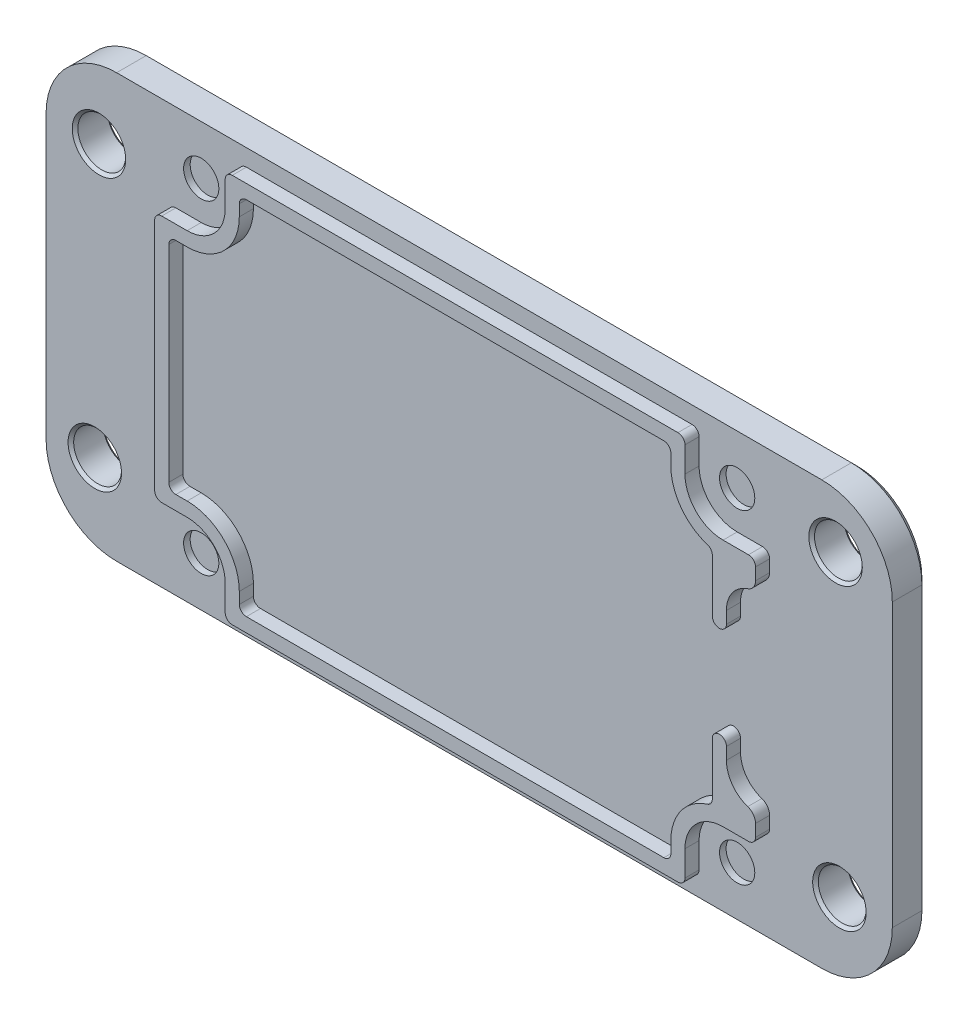
SolidWorks part; units mm, degrees
ref_plane "Plane XZ" through (0, 0, 0) normal (0, 0, 1) x (1, 0, 0)
ref_plane "Plane XY" through (0, 0, 0) normal (0, 1, 0) x (1, 0, 0)
ref_plane "Plane YZ" through (0, 0, 0) normal (1, 0, 0) x (0, 0, -1)
sketch "Sketch1" plane through (0, 0, 0) normal (0, 0, 1) x (1, 0, 0)
  line L0 (0, 19.05) -> (0, -19.05) construction
  line L1 (-38.1, 19.05) -> (38.1, 19.05)
  line L2 (-38.1, 19.05) -> (-38.1, -19.05)
  line L3 (-38.1, -19.05) -> (38.1, -19.05)
  line L4 (38.1, 19.05) -> (38.1, -19.05)
  dimension "D1" = 76.2
  dimension "D2" = 38.1
extrude "Boss-Extrude1" add sketch "Sketch1" along normal blind 3.175
sketch "Sketch2" plane through (0, 0, 3.175) normal (0, 0, 1) x (1, 0, 0)
  line L0 (0, 17.78) -> (0, -17.78) construction
  line L1 (-27.305, 17.78) -> (27.305, 17.78) construction
  line L2 (-27.305, 17.78) -> (-27.305, -17.78) construction
  line L3 (-27.305, -17.78) -> (27.305, -17.78) construction
  line L4 (27.305, 17.78) -> (27.305, -17.78) construction
  line L5 (-27.305, -11.43) -> (-24.13, -11.43)
  line L6 (-20.955, -14.605) -> (-20.955, -17.78)
  line L7 (-27.305, 0) -> (0, 0) construction
  line L8 (27.305, 17.78) -> (27.305, 8.255) construction
  line L9 (24.6862, 8.255) -> (27.305, 8.255) construction
  line L10 (24.6862, 8.255) -> (24.6862, -8.255) construction
  line L11 (27.305, -8.255) -> (24.6862, -8.255) construction
  line L12 (27.305, -8.255) -> (27.305, -17.78) construction
  line L13 (27.305, -11.43) -> (24.13, -11.43)
  line L14 (20.955, -14.605) -> (20.955, -17.78)
  line L15 (-27.305, 11.43) -> (-24.13, 11.43)
  line L16 (-20.955, 14.605) -> (-20.955, 17.78)
  line L17 (27.305, 11.43) -> (24.13, 11.43)
  line L18 (20.955, 14.605) -> (20.955, 17.78)
  line L19 (-20.955, 17.78) -> (20.955, 17.78)
  line L20 (-27.305, -11.43) -> (-27.305, 11.43)
  line L21 (-20.955, -17.78) -> (20.955, -17.78)
  line L22 (27.305, -11.43) -> (27.305, -8.255) construction
  line L23 (27.305, 8.255) -> (27.305, 11.43) construction
  line L24 (27.305, 11.43) -> (27.305, 9.4613)
  line L26 (27.305, -9.4613) -> (27.305, -11.43)
  line L27 (24.6862, -5.8423) -> (24.6862, 5.8423)
  arc A0 (-24.13, -11.43) -> (-20.955, -14.605) centre (-24.13, -14.605) cw
  circle A1 centre (-24.13, -14.605) radius 1.5875 construction
  arc A6 (24.13, -11.43) -> (20.955, -14.605) centre (24.13, -14.605) ccw
  circle A7 centre (24.13, -14.605) radius 1.5875 construction
  arc A8 (-24.13, 11.43) -> (-20.955, 14.605) centre (-24.13, 14.605) ccw
  arc A9 (24.13, 11.43) -> (20.955, 14.605) centre (24.13, 14.605) cw
  circle A10 centre (24.13, 14.605) radius 1.5875 construction
  circle A11 centre (-24.13, 14.605) radius 1.5875 construction
  arc A16 (27.305, 9.4613) -> (26.4321, 8.255) centre (26.035, 9.4613) cw
  arc A17 (26.4321, 8.255) -> (24.6862, 5.8423) centre (27.2262, 5.8423) ccw
  arc A18 (27.305, -9.4613) -> (26.4321, -8.255) centre (26.035, -9.4613) ccw
  arc A19 (26.4321, -8.255) -> (24.6862, -5.8423) centre (27.2262, -5.8423) cw
  point P21 (27.305, -8.255)
  point P24 (27.305, 8.255)
  point P27 (24.6862, 8.255)
  point P30 (24.6862, -8.255)
  dimension "D5" = 3.175
  dimension "D6" = 29.21
  dimension "D7" = 48.26
  dimension "D8" = 3.175
  dimension "D12" = 1.27
  dimension "D13" = 2.54
  dimension "D1" = 54.61
  dimension "D2" = 35.56
  dimension "D3" = 22.86
  dimension "D4" = 41.91
  dimension "D9" = 16.51
  dimension "D10" = 2.6188
sketch "Sketch4" plane through (0, 0, 3.175) normal (0, 0, 1) x (1, 0, 0)
  circle A0 centre (24.13, -14.605) radius 1.5875 construction
  circle A1 centre (24.13, 14.605) radius 1.5875 construction
  circle A2 centre (-24.13, 14.605) radius 1.5875 construction
  circle A3 centre (-24.13, -14.605) radius 1.5875 construction
  circle A4 centre (24.13, -14.605) radius 1.5875
  circle A5 centre (24.13, 14.605) radius 1.5875
  circle A6 centre (-24.13, 14.605) radius 1.5875
  circle A7 centre (-24.13, -14.605) radius 1.5875
extrude "Cut-Extrude1" cut sketch "Sketch4" against normal through all
hole_wizard "CBORE for #2 Pan Head Machine Screw1" positions "Sketch6" profile "Sketch7" counterbore size "#2" standard "ANSI Inch" end condition through all
sketch "Sketch6" plane through (0, 0, 0) normal (0, 0, -1) x (-1, 0, 0)
  circle A0 centre (-24.13, -14.605) radius 1.5875 construction
  circle A1 centre (24.13, -14.605) radius 1.5875 construction
  point P0 (-24.13, 14.605)
  point P3 (-24.13, -14.605)
  point P5 (24.13, -14.605)
  point P7 (24.13, 14.605)
sketch "Sketch7" plane through (24.13, 14.605, 0) normal (1, 0, 0) x (0, 1, 0)
  line L0 (0, 0) -> (0, 3.175)
  line L1 (0, 3.175) -> (1.3525, 3.175)
  line L3 (1.3525, 3.175) -> (1.3525, 2.0828)
  line L4 (2.3812, 2.0828) -> (1.3525, 2.0828)
  line L5 (2.3812, 2.0828) -> (2.3813, 0.3287)
  line L6 (2.3813, 0.3287) -> (2.667, 0)
  line L7 (2.667, 0) -> (0, 0)
  line L8 (-2.3813, 0.3287) -> (-2.667, 0) construction
  line L11 (0, -6.35) -> (0, 107.95) construction
  dimension "Thru Hole Dia." = 2.7051
  dimension "Thru Hole Depth" = 3.175
  dimension "C'Bore Dia." = 4.7625
  dimension "C'Bore Depth" = 2.0828
  dimension "Near C'Sink Dia." = 5.334
  dimension "Near C'Sink Angle" = 82
sketch "Sketch5" plane through (0, 0, 3.175) normal (0, 0, 1) x (1, 0, 0)
  line L0 (19.431, 14.605) -> (19.431, 16.256)
  line L1 (19.431, 16.256) -> (-19.431, 16.256)
  line L2 (-19.431, 16.256) -> (-19.431, 14.605)
  line L3 (-24.13, 9.906) -> (-25.781, 9.906)
  line L4 (-25.781, 9.906) -> (-25.781, -9.906)
  line L5 (-25.781, -9.906) -> (-24.13, -9.906)
  line L6 (-19.431, -14.605) -> (-19.431, -16.256)
  line L7 (-19.431, -16.256) -> (19.431, -16.256)
  line L8 (19.431, -16.256) -> (19.431, -14.605)
  line L9 (23.1622, -10.0068) -> (23.1622, 10.0068)
  line L28 (-27.051, 11.176) -> (-27.051, -11.176)
  line L29 (-27.051, -11.176) -> (-24.13, -11.176)
  line L30 (-20.701, -14.605) -> (-20.701, -17.526)
  line L31 (-20.701, -17.526) -> (20.701, -17.526)
  line L32 (20.701, -17.526) -> (20.701, -14.605)
  line L33 (24.13, -11.176) -> (27.051, -11.176)
  line L34 (27.051, -11.176) -> (27.051, -9.4613)
  line L35 (24.4322, -5.8423) -> (24.4322, 5.8423)
  line L36 (27.051, 9.4613) -> (27.051, 11.176)
  line L37 (27.051, 11.176) -> (24.13, 11.176)
  line L38 (20.701, 14.605) -> (20.701, 17.526)
  line L39 (20.701, 17.526) -> (-20.701, 17.526)
  line L40 (-20.701, 17.526) -> (-20.701, 14.605)
  line L41 (-24.13, 11.176) -> (-27.051, 11.176)
  line L42 (-27.051, 11.176) -> (-27.051, -11.176)
  line L43 (-27.051, -11.176) -> (-24.13, -11.176)
  line L44 (-20.701, -14.605) -> (-20.701, -17.526)
  line L45 (-20.701, -17.526) -> (20.701, -17.526)
  line L46 (20.701, -17.526) -> (20.701, -14.605)
  line L47 (24.13, -11.176) -> (27.051, -11.176)
  line L48 (27.051, -11.176) -> (27.051, -9.4613)
  line L49 (24.4322, -5.8423) -> (24.4322, 5.8423)
  line L50 (27.051, 9.4613) -> (27.051, 11.176)
  line L51 (27.051, 11.176) -> (24.13, 11.176)
  line L52 (20.701, 14.605) -> (20.701, 17.526)
  line L53 (20.701, 17.526) -> (-20.701, 17.526)
  line L54 (-20.701, 17.526) -> (-20.701, 14.605)
  line L55 (-24.13, 11.176) -> (-27.051, 11.176)
  arc A0 (-24.13, 9.906) -> (-19.431, 14.605) centre (-24.13, 14.605) ccw
  arc A1 (-19.431, -14.605) -> (-24.13, -9.906) centre (-24.13, -14.605) ccw
  arc A2 (19.431, 14.605) -> (23.1622, 10.0068) centre (24.13, 14.605) ccw
  arc A3 (19.431, -14.605) -> (23.1622, -10.0068) centre (24.13, -14.605) cw
  arc A16 (-20.701, -14.605) -> (-24.13, -11.176) centre (-24.13, -14.605) ccw
  arc A17 (24.13, -11.176) -> (20.701, -14.605) centre (24.13, -14.605) ccw
  arc A18 (27.051, -9.4613) -> (26.3526, -8.4963) centre (26.035, -9.4613) ccw
  arc A19 (24.4322, -5.8423) -> (26.3526, -8.4963) centre (27.2262, -5.8423) ccw
  arc A20 (26.3526, 8.4963) -> (24.4322, 5.8423) centre (27.2262, 5.8423) ccw
  arc A21 (26.3526, 8.4963) -> (27.051, 9.4613) centre (26.035, 9.4613) ccw
  arc A22 (20.701, 14.605) -> (24.13, 11.176) centre (24.13, 14.605) ccw
  arc A23 (-24.13, 11.176) -> (-20.701, 14.605) centre (-24.13, 14.605) ccw
  arc A24 (-20.701, -14.605) -> (-24.13, -11.176) centre (-24.13, -14.605) ccw
  arc A25 (24.13, -11.176) -> (20.701, -14.605) centre (24.13, -14.605) ccw
  arc A26 (27.051, -9.4613) -> (26.3526, -8.4963) centre (26.035, -9.4613) ccw
  arc A27 (24.4322, -5.8423) -> (26.3526, -8.4963) centre (27.2262, -5.8423) ccw
  arc A28 (26.3526, 8.4963) -> (24.4322, 5.8423) centre (27.2262, 5.8423) ccw
  arc A29 (26.3526, 8.4963) -> (27.051, 9.4613) centre (26.035, 9.4613) ccw
  arc A30 (20.701, 14.605) -> (24.13, 11.176) centre (24.13, 14.605) ccw
  arc A31 (-24.13, 11.176) -> (-20.701, 14.605) centre (-24.13, 14.605) ccw
  dimension "D3" = 1.27
  dimension "D1" = 0.254
  dimension "D2" = 1.27
extrude "Boss-Extrude3" add sketch "Sketch5" along normal blind 1.27 contours A31 L55 L42 L43 A24 L44 L45 L46 A25 L47 L48 A26 A27 L49 A28 A29 L50 L51 A30 L52 L53 L54 A3 L8 L7 L6 A1 L5 L4 L3 A0 L2 L1 L0 A2 L9
fillet "Fillet1" radius 6.35 4 edges at (38.1, -19.05, 1.5875) (38.1, 19.05, 1.5875) (-38.1, 19.05, 1.5875) (-38.1, -19.05, 1.5875)
fillet "Fillet2" radius 0.635 8 edges at (-20.701, 17.526, 3.81) (-27.051, 11.176, 3.81) (-27.051, -11.176, 3.81) (-20.701, -17.526, 3.81) (27.051, -11.176, 3.81) (20.701, -17.526, 3.81) (20.701, 17.526, 3.81) (27.051, 11.176, 3.81)
fillet "Fillet3" radius 0.635 8 edges at (-25.781, -9.906, 3.81) (-19.431, -16.256, 3.81) (19.431, -16.256, 3.81) (23.1622, -10.0068, 3.81) (23.1622, 10.0068, 3.81) (19.431, 16.256, 3.81) (-25.781, 9.906, 3.81) (-19.431, 16.256, 3.81)
hole_wizard "#6 Clearance Hole1" positions "Sketch9" profile "Sketch10" hole size "#6" standard "ANSI Inch" end condition through all
sketch "Sketch9" plane through (0, 0, 3.175) normal (0, 0, 1) x (1, 0, 0)
  line L1 (-33.3375, 12.7) -> (33.3375, 12.7) construction
  line L2 (-33.3375, 12.7) -> (-33.3375, -12.7) construction
  line L3 (-33.3375, -12.7) -> (33.3375, -12.7) construction
  line L4 (33.3375, 12.7) -> (33.3375, -12.7) construction
  line L5 (-38.1, 12.7) -> (-38.1, -12.7) construction
  line L6 (-33.3375, 0) -> (33.3375, 0) construction
  point P0 (-33.3375, 12.7)
  point P2 (-33.7144, -11.9542)
  point P4 (32.9919, 14.0391)
  point P6 (33.3375, -12.7)
  dimension "D1" = 4.7625
  dimension "D2" = 25.4
sketch "Sketch10" plane through (-33.3375, 12.7, 3.175) normal (1, 0, 0) x (0, -1, 0)
  line L0 (0, 0) -> (0, 3.175)
  line L1 (0, 3.175) -> (2.1526, 3.175)
  line L2 (2.1526, 3.175) -> (2.1526, 0)
  line L5 (2.1526, 0) -> (0, 0)
  line L11 (0, -6.35) -> (0, 107.95) construction
  dimension "Thru Hole Dia." = 4.3053
  dimension "Thru Hole Depth" = 3.175
chamfer "Chamfer1" distance 0.508 angle 45 8 edges at (0, 19.05, 0) (-36.2401, 17.1901, 0) (36.2401, 17.1901, 0) (-38.1, 0, 0) (38.1, 0, 0) (-36.2401, -17.1901, 0) (36.2401, -17.1901, 0) (0, -19.05, 0)
chamfer "Chamfer2" distance 0.254 angle 45 8 edges at (-31.5617, -11.9542, 3.175) (-31.5617, -11.9542, 0) (-31.1849, 12.7, 3.175) (-31.1849, 12.7, 0) (35.1446, 14.0391, 3.175) (35.1446, 14.0391, 0) (35.4901, -12.7, 3.175) (35.4901, -12.7, 0)
sketch "Sketch11" plane through (0, 0, 3.175) normal (0, 0, 1) x (1, 0, 0)
  line L0 (24.4322, 0) -> (23.1622, 0) construction
  line L1 (24.4322, 4.7625) -> (23.1622, 4.7625) construction
  line L2 (24.4322, 4.7625) -> (24.4322, -4.7625)
  line L3 (24.4322, -4.7625) -> (23.1622, -4.7625) construction
  line L4 (23.1622, 4.7625) -> (23.1622, -4.7625)
  line L5 (24.4322, -5.8423) -> (24.4322, 5.8423) construction
  line L6 (23.1622, -9.5175) -> (23.1622, 9.5175) construction
  arc A0 (24.4322, 4.7625) -> (23.1622, 4.7625) centre (23.7972, 4.7625) cw
  arc A1 (24.4322, -4.7625) -> (23.1622, -4.7625) centre (23.7972, -4.7625) ccw
  dimension "D1" = 9.525
extrude "Cut-Extrude2" cut sketch "Sketch11" along normal through all
sketch "Sketch12" plane through (0, 0, 2.0828) normal (0, 0, -1) x (-1, 0, 0)
  circle A0 centre (-24.13, 14.605) radius 1.5875 construction
  circle A1 centre (-24.13, 14.605) radius 1.5875
  circle A2 centre (24.13, 14.605) radius 1.5875 construction
  circle A3 centre (24.13, 14.605) radius 1.5875
  circle A4 centre (24.13, -14.605) radius 1.5875 construction
  circle A5 centre (24.13, -14.605) radius 1.5875
  circle A6 centre (-24.13, -14.605) radius 1.5875 construction
  circle A7 centre (-24.13, -14.605) radius 1.5875
extrude "Boss-Extrude4" add sketch "Sketch12" against normal blind 0.5
